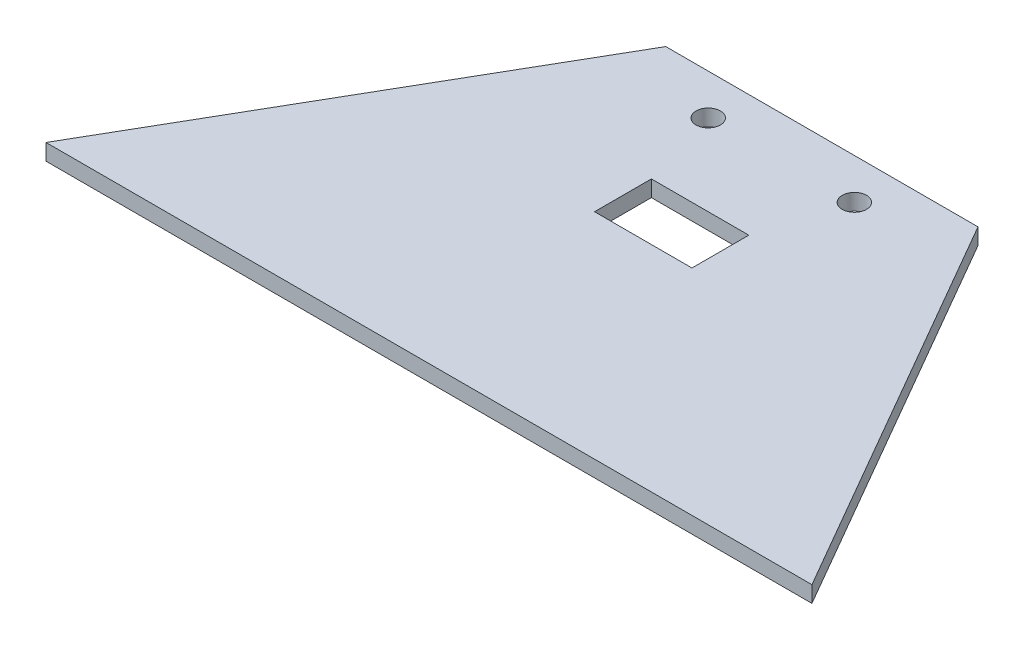
SolidWorks part; units mm, degrees
ref_plane "Plan de face" through (0, 0, 0) normal (0, 0, 1) x (1, 0, 0)
ref_plane "Plan de dessus" through (0, 0, 0) normal (0, 1, 0) x (1, 0, 0)
ref_plane "Plan de droite" through (0, 0, 0) normal (1, 0, 0) x (0, 0, -1)
sketch "Esquisse1" plane through (0, 0, 0) normal (0, 1, 0) x (1, 0, 0)
  line L0 (-5.0906, 24.1327) -> (6.9094, 24.1327)
  line L1 (-18.3171, 39.1327) -> (20.1359, 39.1327)
  line L2 (0.9094, 24.1327) -> (0.9094, 39.1327) construction
  line L3 (-46.2557, -9.2583) -> (48.0744, -9.2583)
  line L4 (-18.3171, 39.1327) -> (-18.3171, -9.2583) construction
  line L5 (13.9094, 39.1327) -> (-12.0906, 39.1327) construction
  line L6 (25.9094, 24.1327) -> (-24.0906, 24.1327) construction
  line L7 (-46.2557, -9.2583) -> (-18.3171, 39.1327)
  line L8 (48.0744, -9.2583) -> (20.1359, 39.1327)
  line L9 (6.9094, 24.1327) -> (6.9094, 17.1327)
  line L10 (6.9094, 17.1327) -> (-5.0906, 17.1327)
  line L11 (-5.0906, 24.1327) -> (-5.0906, 17.1327)
  circle A0 centre (-8.0906, 34.1327) radius 1.5
  circle A1 centre (9.9094, 34.1327) radius 1.5
  point P0 (0, 0)
  point P4 (0.9094, -9.2583)
  point P15 (0.9094, -9.2583)
  point P27 (0.9094, 17.1327)
  dimension "D3" = 3
  dimension "D4" = 3
  dimension "D1" = 0
  dimension "D2" = 30
  dimension "D5" = 6
  dimension "D6" = 7
extrude "Boss.-Extru.1" add sketch "Esquisse1" along normal blind 2
